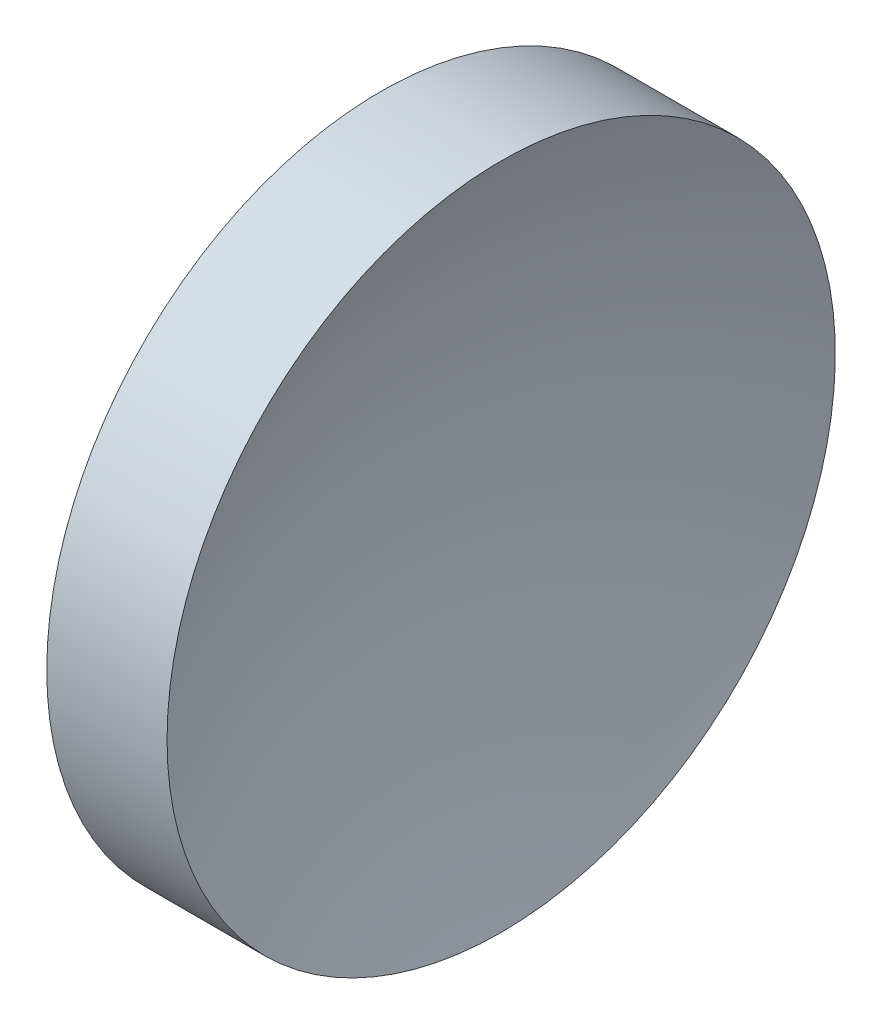
SolidWorks part; units mm, degrees
ref_plane "前视基准面" through (0, 0, 0) normal (0, 0, 1) x (1, 0, 0)
ref_plane "上视基准面" through (0, 0, 0) normal (0, 1, 0) x (1, 0, 0)
ref_plane "右视基准面" through (0, 0, 0) normal (1, 0, 0) x (0, 0, -1)
sketch "草图1" plane through (0, 0, 0) normal (0, 0, 1) x (1, 0, 0)
  line L0 (56.1009, 32.6108) -> (68.2773, 32.6108) construction
  line L1 (57.5323, 32.6108) -> (57.5323, 45.1108)
  line L2 (57.5323, 45.1108) -> (62.0323, 45.1108)
  line L3 (59.5323, 32.6108) -> (57.5323, 32.6108)
  arc A0 (62.0323, 45.1108) -> (59.5323, 32.6108) centre (92.0323, 32.6108) ccw
revolve "旋转1" add sketch "草图1" angle 360 about L0
